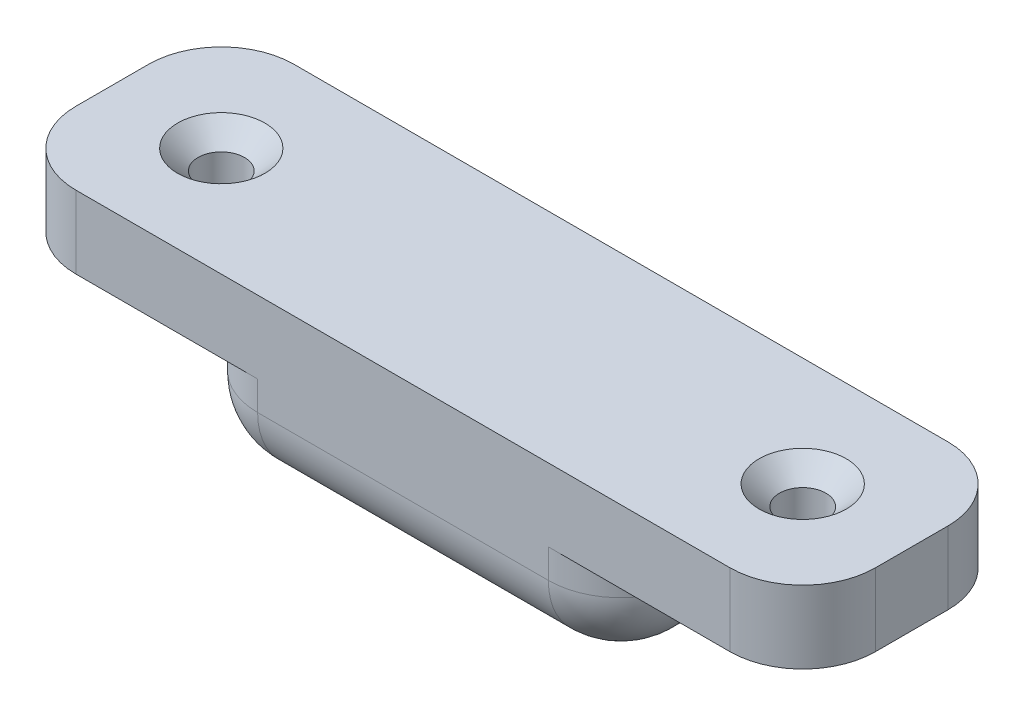
SolidWorks part; units mm, degrees
ref_plane "Plan de face" through (0, 0, 0) normal (0, 0, 1) x (1, 0, 0)
ref_plane "Plan de dessus" through (0, 0, 0) normal (0, 1, 0) x (1, 0, 0)
ref_plane "Plan de droite" through (0, 0, 0) normal (1, 0, 0) x (0, 0, -1)
sketch "Esquisse1" plane through (0, 0, 0) normal (0, 0, 1) x (1, 0, 0)
  line L0 (27.5, 6) -> (-27.5, 6)
  line L1 (-27.5, 6) -> (-27.5, 1)
  line L2 (-27.5, 1) -> (-15, 1)
  line L3 (-15, 1) -> (-15, -6)
  line L4 (-15, -6) -> (15, -6)
  line L5 (0, 6) -> (0, -6) construction
  line L6 (15, 1) -> (15, -6)
  line L7 (27.5, 1) -> (15, 1)
  line L8 (27.5, 6) -> (27.5, 1)
  point P2 (0, 0)
  dimension "D1" = 7
  dimension "D2" = 5
  dimension "D3" = 15
  dimension "D4" = 12.5
extrude "Boss.-Extru.1" add sketch "Esquisse1" along normal blind 15
hole_wizard "Fraisage pour vis à tête fraisée cruciforme M31" positions "Esquisse2" profile "Esquisse3" countersink size "M3" standard "AS" end condition through all
sketch "Esquisse2" plane through (0, 6, 0) normal (0, 1, 0) x (1, 0, 0)
  line L0 (-20, -7.5) -> (20, -7.5)
  line L2 (-27.5, -15) -> (-27.5, 0) construction
  point P0 (-20, -7.5)
  point P2 (20, -7.5)
  point P10 (-27.5, -7.5)
  point P16 (0, -7.5)
  dimension "D1" = 40
sketch "Esquisse3" plane through (-20, 6, 7.5) normal (1, 0, 0) x (0, 0, 1)
  line L0 (0, 0) -> (0, 12)
  line L1 (0, 12) -> (1.6, 12)
  line L2 (1.6, 12) -> (1.6, 1.352)
  line L3 (1.6, 1.352) -> (3, 0)
  line L5 (3, 0) -> (0, 0)
  line L6 (-1.6, 1.352) -> (-3, 0) construction
  line L11 (0, -6.35) -> (0, 107.95) construction
  dimension "Diamètre du perçage jusqu'au prochain" = 3.2
  dimension "Profondeur du perçage jusqu'au prochain" = 12
  dimension "Diamètre du fraisage entrant" = 6
  dimension "Angle du fraisage entrant" = 92
fillet "Congé2" radius 5 12 edges at (-27.5, 3.5, 0) (-27.5, 3.5, 15) (27.5, 3.5, 0) (27.5, 3.5, 15) (15, -2.5, 15) (15, -2.5, 0) (-15, -2.5, 0) (-15, -2.5, 15) (0, -6, 0) (-15, -6, 7.5) (0, -6, 15) (15, -6, 7.5)
